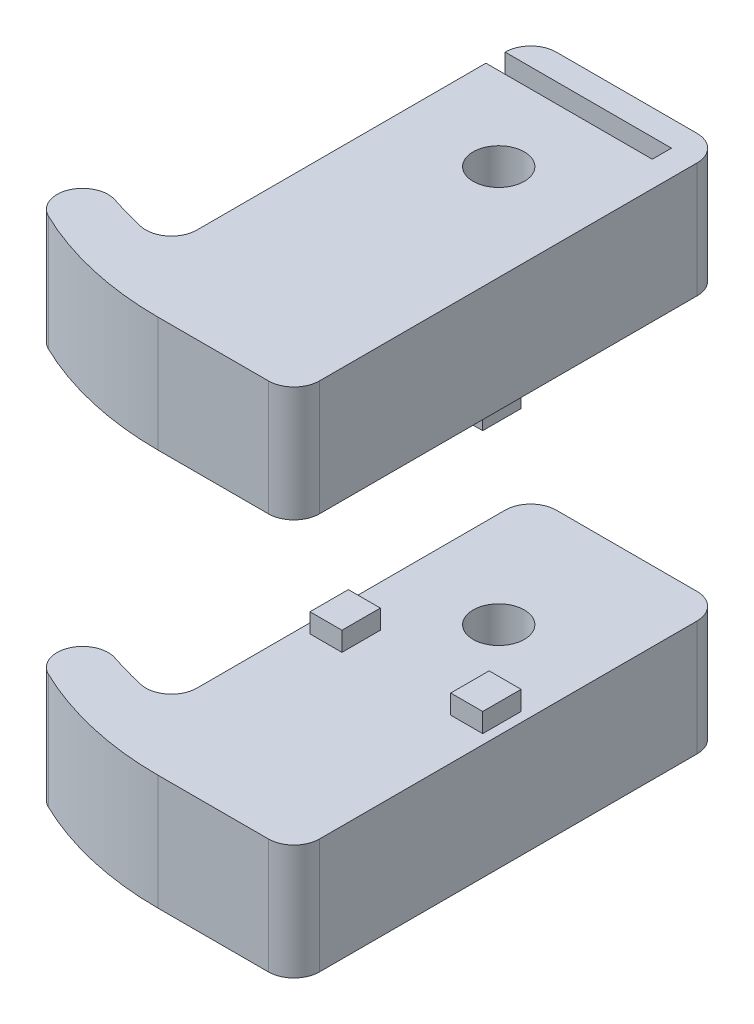
SolidWorks part; units mm, degrees
ref_plane "前视基准面" through (0, 0, 0) normal (0, 0, 1) x (1, 0, 0)
ref_plane "上视基准面" through (0, 0, 0) normal (0, 1, 0) x (1, 0, 0)
ref_plane "右视基准面" through (0, 0, 0) normal (1, 0, 0) x (0, 0, -1)
other "Configuration Table"
sketch "草图1" plane through (0, 0, 0) normal (0, 1, 0) x (1, 0, 0)
  line L0 (-2.3828, 33.5) -> (8.6172, 33.5)
  line L1 (10.6172, 31.5) -> (10.6172, 2)
  line L2 (8.6172, 0) -> (0, 0)
  line L5 (-4.3828, 7.4211) -> (-4.3828, 31.5)
  arc A0 (0, 0) -> (-11.1311, 2.5577) centre (0, 25.5) cw
  arc A1 (-6.8364, 5.4732) -> (-9.6333, 6.257) centre (0.5711, 37.2861) cw
  arc A2 (-11.1311, 2.5577) -> (-9.6333, 6.257) centre (-10.2581, 4.3571) cw
  arc A3 (-6.8364, 5.4732) -> (-4.3828, 7.4211) centre (-6.3828, 7.4211) ccw
  arc A4 (10.6172, 2) -> (8.6172, 0) centre (8.6172, 2) cw
  arc A5 (8.6172, 33.5) -> (10.6172, 31.5) centre (8.6172, 31.5) cw
  arc A6 (-2.3828, 33.5) -> (-4.3828, 31.5) centre (-2.3828, 31.5) ccw
  circle A7 centre (3.1172, 23.5) radius 2
  point P15 (10.6172, 0)
  point P18 (10.6172, 33.5)
  point P21 (-4.3828, 33.5)
  point P24 (3.1172, 33.5)
  dimension "D5" = 25.5
  dimension "D3" = 2
  dimension "D4" = 2
  dimension "D6" = 4
  dimension "D1" = 15
  dimension "D2" = 33.5
  dimension "D7" = 10
  dimension "D8" = 8.6172
extrude "凸台-拉伸1" add sketch "草图1" along normal blind 9
sketch "草图3" plane through (0, 9, 0) normal (0, 1, 0) x (1, 0, 0)
  line L0 (-4.3828, 31.5) -> (-4.3828, 7.4211) construction
  line L1 (-3.6328, 18.5) -> (-1.1328, 18.5)
  line L2 (-3.6328, 18.5) -> (-3.6328, 15.5)
  line L3 (-3.6328, 15.5) -> (-1.1328, 15.5)
  line L4 (-1.1328, 18.5) -> (-1.1328, 15.5)
  line L5 (3.1172, 23.5) -> (3.1172, 23.4622) construction
  line L6 (7.3672, 18.5) -> (7.3672, 15.5)
  line L7 (9.8672, 15.5) -> (7.3672, 15.5)
  line L8 (9.8672, 18.5) -> (9.8672, 15.5)
  line L9 (9.8672, 18.5) -> (7.3672, 18.5)
  circle A0 centre (3.1172, 23.5) radius 2 construction
  circle A1 centre (3.1172, 23.5) radius 2 construction
  dimension "D1" = 2.5
  dimension "D2" = 3
  dimension "D3" = 0.75
  dimension "D4" = 5
extrude "凸台-拉伸2" add sketch "草图3" along normal blind 1.5
sketch "草图5" plane through (0, 9, 0) normal (0, 1, 0) x (1, 0, 0)
  line L0 (8.6172, 33.5) -> (-2.3828, 33.5) construction
  line L1 (-4.3828, 31.5) -> (8.6172, 31.5)
  line L2 (-4.3828, 31.5) -> (-4.3828, 30)
  line L3 (-4.3828, 30) -> (8.6172, 30)
  line L4 (8.6172, 31.5) -> (8.6172, 30)
  line L6 (-4.3828, 31.5) -> (-4.3828, 7.4211) construction
  dimension "D1" = 1.5
  dimension "D2" = 13
  dimension "D3" = 2
extrude "切除-拉伸1" cut sketch "草图5" against normal up to next from offset 2 offset against normal yes
mirror "镜向8" about plane through (0, 0, -25.5) normal (0, -1, 0) of bodies 108 109
sketch "草图9" plane through (0, 0, 0) normal (0, 1, 0) x (1, 0, 0)
  line L1 (-24.5545, 37.01) -> (24.9915, 37.01)
  line L2 (-24.5545, 37.01) -> (-24.5545, -5.1983)
  line L3 (-24.5545, -5.1983) -> (24.9915, -5.1983)
  line L4 (24.9915, 37.01) -> (24.9915, -5.1983)
extrude "切除-拉伸2" cut sketch "草图9" against normal through all
ref_plane "基准面1" through (0, 20, 0) normal (0, -1, 0) x (-1, 0, 0)
mirror "镜向11" about plane through (0, 20, 0) normal (0, -1, 0) of bodies 112
